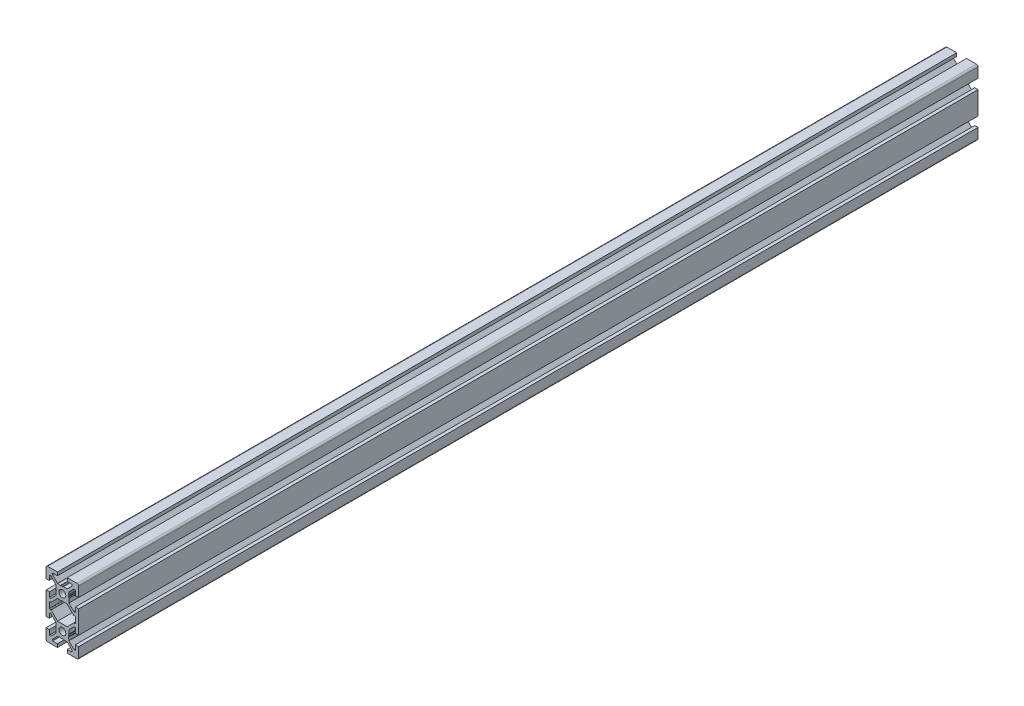
SolidWorks part; units mm, degrees
ref_plane "Front Plane" through (0, 0, 0) normal (0, 0, 1) x (1, 0, 0)
ref_plane "Top Plane" through (0, 0, 0) normal (0, 1, 0) x (1, 0, 0)
ref_plane "Right Plane" through (0, 0, 0) normal (1, 0, 0) x (0, 0, -1)
ref_plane "Plane1" through (0, 0, -600) normal (0, 0, -1) x (-1, 0, 0)
sketch "Sketch1" plane through (0, 0, -600) normal (0, 0, -1) x (-1, 0, 0)
  line L0 (8, 1.7) -> (8, -1.7)
  line L1 (7.7, -2) -> (7.0636, -2)
  line L2 (6.8515, -2.0879) -> (2.9393, -6)
  line L3 (2.9393, -6) -> (-2.9393, -6)
  line L4 (-2.9393, -6) -> (-6.8515, -2.0879)
  line L5 (-7.0636, -2) -> (-7.7, -2)
  line L6 (-8, -1.7) -> (-8, 1.7)
  line L7 (-7.7, 2) -> (-7.0636, 2)
  line L8 (-6.8515, 2.0879) -> (-2.9393, 6)
  line L9 (-2.9393, 6) -> (2.9393, 6)
  line L10 (2.9393, 6) -> (6.8515, 2.0879)
  line L11 (7.0636, 2) -> (7.7, 2)
  line L12 (10, -7) -> (10, 7)
  line L13 (10, 7) -> (8, 7)
  line L14 (8, 7) -> (8, 4)
  line L15 (8, 4) -> (7.0607, 4)
  line L16 (7.0607, 4) -> (4, 7.0607)
  line L17 (4, 7.0607) -> (4, 7.5)
  line L18 (4, 7.5) -> (3.751, 8.7811)
  line L19 (3.751, 8.7811) -> (3.933, 9.0964)
  line L20 (3.933, 9.5964) -> (3.7, 10)
  line L21 (3.7, 10) -> (3.933, 10.4036)
  line L22 (4, 10.6536) -> (4, 12.9393)
  line L23 (4, 12.9393) -> (7.0607, 16)
  line L24 (7.0607, 16) -> (8, 16)
  line L25 (8, 16) -> (8, 13)
  line L26 (8, 13) -> (10, 13)
  line L27 (10, 13) -> (10, 19)
  line L28 (9, 20) -> (3, 20)
  line L29 (3, 20) -> (3, 18)
  line L30 (3, 18) -> (6, 18)
  line L31 (6, 18) -> (6, 17.0607)
  line L32 (6, 17.0607) -> (2.9393, 14)
  line L33 (2.9393, 14) -> (2.5, 14)
  line L34 (2.5, 14) -> (1.2189, 13.751)
  line L35 (1.2189, 13.751) -> (0.9036, 13.933)
  line L36 (0.4036, 13.933) -> (0, 13.7)
  line L37 (0, 13.7) -> (-0.4036, 13.933)
  line L38 (-0.6536, 14) -> (-2.9393, 14)
  line L39 (-2.9393, 14) -> (-6, 17.0607)
  line L40 (-6, 17.0607) -> (-6, 18)
  line L41 (-6, 18) -> (-3, 18)
  line L42 (-3, 18) -> (-3, 20)
  line L43 (-3, 20) -> (-9, 20)
  line L44 (-10, 19) -> (-10, 13)
  line L45 (-10, 13) -> (-8, 13)
  line L46 (-8, 13) -> (-8, 16)
  line L47 (-8, 16) -> (-7.0607, 16)
  line L48 (-7.0607, 16) -> (-4, 12.9393)
  line L49 (-4, 12.9393) -> (-4, 12.5)
  line L50 (-4, 12.5) -> (-3.751, 11.2189)
  line L51 (-3.751, 11.2189) -> (-3.933, 10.9036)
  line L52 (-3.933, 10.4036) -> (-3.7, 10)
  line L53 (-3.7, 10) -> (-3.933, 9.5964)
  line L54 (-4, 9.3464) -> (-4, 7.0607)
  line L55 (-4, 7.0607) -> (-7.0607, 4)
  line L56 (-7.0607, 4) -> (-8, 4)
  line L57 (-8, 4) -> (-8, 7)
  line L58 (-8, 7) -> (-10, 7)
  line L59 (-10, 7) -> (-10, -7)
  line L60 (-10, -7) -> (-8, -7)
  line L61 (-8, -7) -> (-8, -4)
  line L62 (-8, -4) -> (-7.0607, -4)
  line L63 (-7.0607, -4) -> (-4, -7.0607)
  line L64 (-4, -7.0607) -> (-4, -9.3464)
  line L65 (-3.933, -9.5964) -> (-3.7, -10)
  line L66 (-3.7, -10) -> (-3.933, -10.4036)
  line L67 (-3.933, -10.9036) -> (-3.751, -11.2189)
  line L68 (-3.751, -11.2189) -> (-4, -12.5)
  line L69 (-4, -12.5) -> (-4, -12.9393)
  line L70 (-4, -12.9393) -> (-7.0607, -16)
  line L71 (-7.0607, -16) -> (-8, -16)
  line L72 (-8, -16) -> (-8, -13)
  line L73 (-8, -13) -> (-10, -13)
  line L74 (-10, -13) -> (-10, -19)
  line L75 (-9, -20) -> (-3, -20)
  line L76 (-3, -20) -> (-3, -18)
  line L77 (-3, -18) -> (-6, -18)
  line L78 (-6, -18) -> (-6, -17.0607)
  line L79 (-6, -17.0607) -> (-2.9393, -14)
  line L80 (-2.9393, -14) -> (-0.6536, -14)
  line L81 (-0.4036, -13.933) -> (0, -13.7)
  line L82 (0, -13.7) -> (0.4036, -13.933)
  line L83 (0.9036, -13.933) -> (1.2189, -13.751)
  line L84 (1.2189, -13.751) -> (2.5, -14)
  line L85 (2.5, -14) -> (2.9393, -14)
  line L86 (2.9393, -14) -> (6, -17.0607)
  line L87 (6, -17.0607) -> (6, -18)
  line L88 (6, -18) -> (3, -18)
  line L89 (3, -18) -> (3, -20)
  line L90 (3, -20) -> (9, -20)
  line L91 (10, -19) -> (10, -13)
  line L92 (10, -13) -> (8, -13)
  line L93 (8, -13) -> (8, -16)
  line L94 (8, -16) -> (7.0607, -16)
  line L95 (7.0607, -16) -> (4, -12.9393)
  line L96 (4, -12.9393) -> (4, -10.6536)
  line L97 (3.933, -10.4036) -> (3.7, -10)
  line L98 (3.7, -10) -> (3.933, -9.5964)
  line L99 (3.933, -9.0964) -> (3.751, -8.7811)
  line L100 (3.751, -8.7811) -> (4, -7.5)
  line L101 (4, -7.5) -> (4, -7.0607)
  line L102 (4, -7.0607) -> (7.0607, -4)
  line L103 (7.0607, -4) -> (8, -4)
  line L104 (8, -4) -> (8, -7)
  line L105 (8, -7) -> (10, -7)
  circle A0 centre (0, -10) radius 2.1
  circle A1 centre (0, 10) radius 2.1
  arc A2 (7.7, 2) -> (8, 1.7) centre (7.7, 1.7) cw
  arc A3 (8, -1.7) -> (7.7, -2) centre (7.7, -1.7) cw
  arc A4 (7.0636, -2) -> (6.8515, -2.0879) centre (7.0636, -2.3) ccw
  arc A5 (-6.8515, -2.0879) -> (-7.0636, -2) centre (-7.0636, -2.3) ccw
  arc A6 (-7.7, -2) -> (-8, -1.7) centre (-7.7, -1.7) cw
  arc A7 (-8, 1.7) -> (-7.7, 2) centre (-7.7, 1.7) cw
  arc A8 (-7.0636, 2) -> (-6.8515, 2.0879) centre (-7.0636, 2.3) ccw
  arc A9 (6.8515, 2.0879) -> (7.0636, 2) centre (7.0636, 2.3) ccw
  arc A10 (3.933, 9.0964) -> (3.933, 9.5964) centre (3.5, 9.3464) ccw
  arc A11 (3.933, 10.4036) -> (4, 10.6536) centre (3.5, 10.6536) ccw
  arc A12 (10, 19) -> (9, 20) centre (9, 19) ccw
  arc A13 (0.9036, 13.933) -> (0.4036, 13.933) centre (0.6536, 13.5) ccw
  arc A14 (-0.4036, 13.933) -> (-0.6536, 14) centre (-0.6536, 13.5) ccw
  arc A15 (-9, 20) -> (-10, 19) centre (-9, 19) ccw
  arc A16 (-3.933, 10.9036) -> (-3.933, 10.4036) centre (-3.5, 10.6536) ccw
  arc A17 (-3.933, 9.5964) -> (-4, 9.3464) centre (-3.5, 9.3464) ccw
  arc A18 (-4, -9.3464) -> (-3.933, -9.5964) centre (-3.5, -9.3464) ccw
  arc A19 (-3.933, -10.4036) -> (-3.933, -10.9036) centre (-3.5, -10.6536) ccw
  arc A20 (-10, -19) -> (-9, -20) centre (-9, -19) ccw
  arc A21 (-0.6536, -14) -> (-0.4036, -13.933) centre (-0.6536, -13.5) ccw
  arc A22 (0.4036, -13.933) -> (0.9036, -13.933) centre (0.6536, -13.5) ccw
  arc A23 (9, -20) -> (10, -19) centre (9, -19) ccw
  arc A24 (4, -10.6536) -> (3.933, -10.4036) centre (3.5, -10.6536) ccw
  arc A25 (3.933, -9.5964) -> (3.933, -9.0964) centre (3.5, -9.3464) ccw
  dimension "D1" = 4.2
  dimension "D3" = 0.3
  dimension "D4" = 0.3
  dimension "D5" = 0.3
  dimension "D6" = 0.3
  dimension "D7" = 0.3
  dimension "D8" = 0.3
  dimension "D9" = 0.3
  dimension "D10" = 0.5
  dimension "D11" = 0.5
  dimension "D12" = 1
  dimension "D13" = 0.5
  dimension "D14" = 0.5
  dimension "D15" = 1
  dimension "D16" = 0.5
  dimension "D17" = 0.5
  dimension "D18" = 0.5
  dimension "D19" = 0.5
  dimension "D20" = 0.4036
  dimension "D21" = 0.5
  dimension "D22" = 0.5
  dimension "D23" = 1
  dimension "D24" = 0.5
  dimension "D25" = 0.5
  dimension "D26" = 0.4036
  dimension "D27" = 0.6536
  dimension "D28" = 0.6536
  dimension "D29" = 0.9036
  dimension "D30" = 0.9036
  dimension "D31" = 1.2189
  dimension "D32" = 1.2189
  dimension "D33" = 2.5
  dimension "D34" = 2.5
  dimension "D35" = 2.9393
  dimension "D36" = 2.9393
  dimension "D37" = 3
  dimension "D38" = 3.5
  dimension "D39" = 6
  dimension "D40" = 6.8515
  dimension "D41" = 3.7
  dimension "D42" = 3.7
  dimension "D43" = 3.751
  dimension "D44" = 3.751
  dimension "D45" = 3.933
  dimension "D46" = 3.933
  dimension "D47" = 6.8515
  dimension "D48" = 7.0607
  dimension "D49" = 7.0607
  dimension "D50" = 7.0636
  dimension "D51" = 7.0636
  dimension "D52" = 8
  dimension "D53" = 10
  dimension "D54" = 3
  dimension "D55" = 4
  dimension "D56" = 6
  dimension "D57" = 6.8515
  dimension "D58" = 6.8515
  dimension "D59" = 7.0607
  dimension "D60" = 7.0607
  dimension "D61" = 0.4036
  dimension "D62" = 0.4036
  dimension "D63" = 0.6536
  dimension "D64" = 0.6536
  dimension "D65" = 2.9393
  dimension "D66" = 2.9393
  dimension "D67" = 8
  dimension "D68" = 2
  dimension "D69" = 3.5
  dimension "D70" = 3.5
  dimension "D71" = 3.7
  dimension "D72" = 3.7
  dimension "D73" = 3.751
  dimension "D74" = 3.751
  dimension "D75" = 3.933
  dimension "D76" = 3.933
  dimension "D77" = 4
  dimension "D78" = 6
  dimension "D79" = 7
  dimension "D80" = 7.0607
  dimension "D81" = 7.0607
  dimension "D82" = 7.5
  dimension "D83" = 8.7811
  dimension "D84" = 9.0964
  dimension "D85" = 9.3464
  dimension "D86" = 9.3464
  dimension "D87" = 9.5964
  dimension "D88" = 9.5964
  dimension "D89" = 10.4036
  dimension "D90" = 12.5
  dimension "D91" = 13
  dimension "D92" = 13.5
  dimension "D93" = 13.5
  dimension "D94" = 18
  dimension "D95" = 20
  dimension "D96" = 2
  dimension "D97" = 4
  dimension "D98" = 6
  dimension "D99" = 7
  dimension "D100" = 7.0607
  dimension "D101" = 7.0607
  dimension "D102" = 7.5
  dimension "D103" = 8.7811
  dimension "D104" = 9.0964
  dimension "D105" = 9.3464
  dimension "D106" = 9.3464
  dimension "D107" = 9.5964
  dimension "D108" = 9.5964
  dimension "D109" = 10.4036
  dimension "D110" = 12.5
  dimension "D111" = 13
  dimension "D112" = 18
extrude "Boss-Extrude1" add sketch "Sketch1" against normal blind 550
